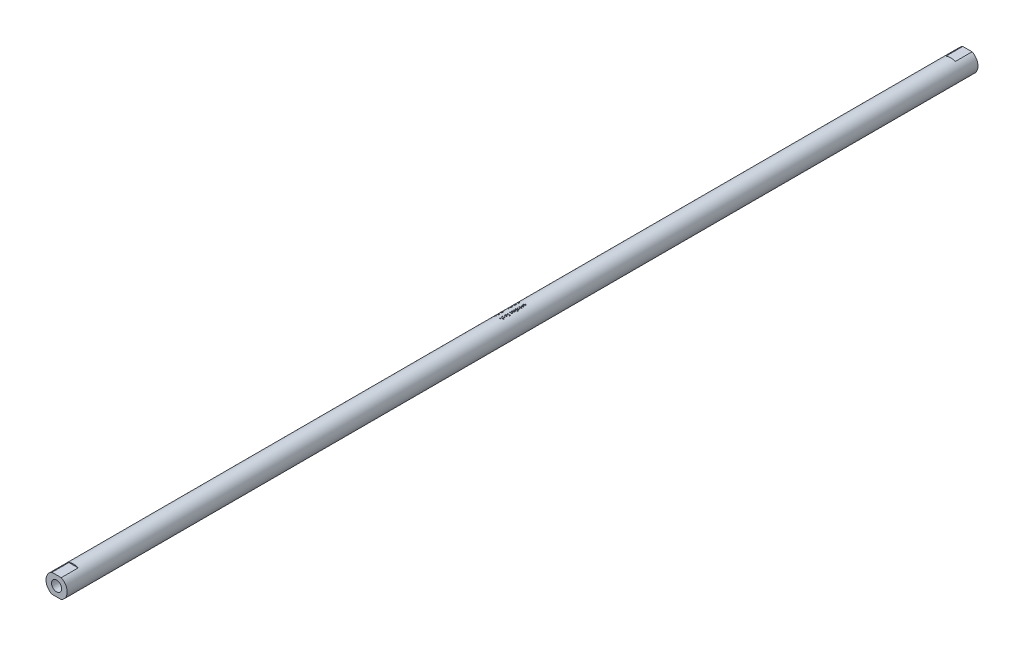
SolidWorks part; units mm, degrees
material "201 Acier inoxydable recuit (SS)"
ref_plane "Plan de face" through (0, 0, 0) normal (0, 0, 1) x (1, 0, 0)
ref_plane "Plan de dessus" through (0, 0, 0) normal (0, 1, 0) x (1, 0, 0)
ref_plane "Plan de droite" through (0, 0, 0) normal (1, 0, 0) x (0, 0, -1)
sketch "Esquisse1" plane through (0, 0, 0) normal (0, 0, 1) x (1, 0, 0)
  circle A0 centre (0, 0) radius 4.99
  dimension "D1" = 9.98
extrude "Boss.-Extru.1" add sketch "Esquisse1" along normal blind 430 from offset 215 offset against normal yes
sketch "Esquisse3" plane through (0, 0, -215) normal (0, 0, -1) x (-1, 0, 0)
  line L1 (-2.3639, 5.2877) -> (2.7677, 5.2877)
  line L2 (-2.3639, 5.2877) -> (-2.3639, 4.48)
  line L3 (-2.3639, 4.48) -> (2.7677, 4.48)
  line L4 (2.7677, 5.2877) -> (2.7677, 4.48)
  line L5 (-3.0927, -4.48) -> (2.8662, -4.48)
  line L6 (-3.0927, -4.48) -> (-3.0927, -5.6619)
  line L7 (-3.0927, -5.6619) -> (2.8662, -5.6619)
  line L8 (2.8662, -4.48) -> (2.8662, -5.6619)
  dimension "D1" = 4.48
  dimension "D2" = 4.48
extrude "Enlèv. mat.-Extru.2" cut sketch "Esquisse3" against normal blind 8
hole_wizard "Trou pour taraudage pour trou taraudé M61" positions "Esquisse5" profile "Esquisse4" hole size "M6" standard "ISO"
sketch "Esquisse5" plane through (0, 0, -215) normal (0, 0, -1) x (-1, 0, 0)
  point P0 (0, 0)
sketch "Esquisse4" plane through (0, 0, -215) normal (1, 0, 0) x (0, 1, 0)
  line L0 (0, 0) -> (0, 26.5022)
  line L1 (0, 26.5022) -> (2.5, 25)
  line L2 (2.5, 25) -> (2.5, 0)
  line L5 (2.5, 0) -> (0, 0)
  line L10 (0, 26.5022) -> (-2.5, 25) construction
  line L11 (0, -6.35) -> (0, 107.95) construction
  dimension "Diamètre du perçage" = 5
  dimension "Profondeur du perçage" = 25
  dimension "Angle de pointe" = 118
sketch "Esquisse7" plane through (0, 0, -215) normal (0, 0, -1) x (-1, 0, 0)
  circle A0 centre (0, 0) radius 2.4
  circle A1 centre (0, 0) radius 2.5 construction
  circle A2 centre (0, 0) radius 2.4
  circle M1 centre (0, 0) radius 2.5
  dimension "D1" = 0.1
extrude "Boss.-Extru.2" add sketch "Esquisse7" against normal blind 15 contours A0 M1
mirror "Symétrie1" about plane through (0, 0, 0) normal (0, 0, 1) of "Enlèv. mat.-Extru.2", "Trou pour taraudage pour trou taraudé M61", "Boss.-Extru.2"
sketch "Esquisse8" plane through (0, 4.48, 0) normal (0, 1, 0) x (1, 0, 0)
  line L0 (0, 215) -> (0, -215) construction
  line L1 (-2.1977, 215) -> (2.1977, 215) construction
  line L2 (2.1977, -215) -> (-2.1977, -215) construction
  text T0 "eMotion Tech\r\nCC BY-NC-SA" font "Century Gothic" height in points 5
extrude "Enlèv. mat.-Extru.3" cut sketch "Esquisse8" against normal blind 1.5 and the other way blind 10
